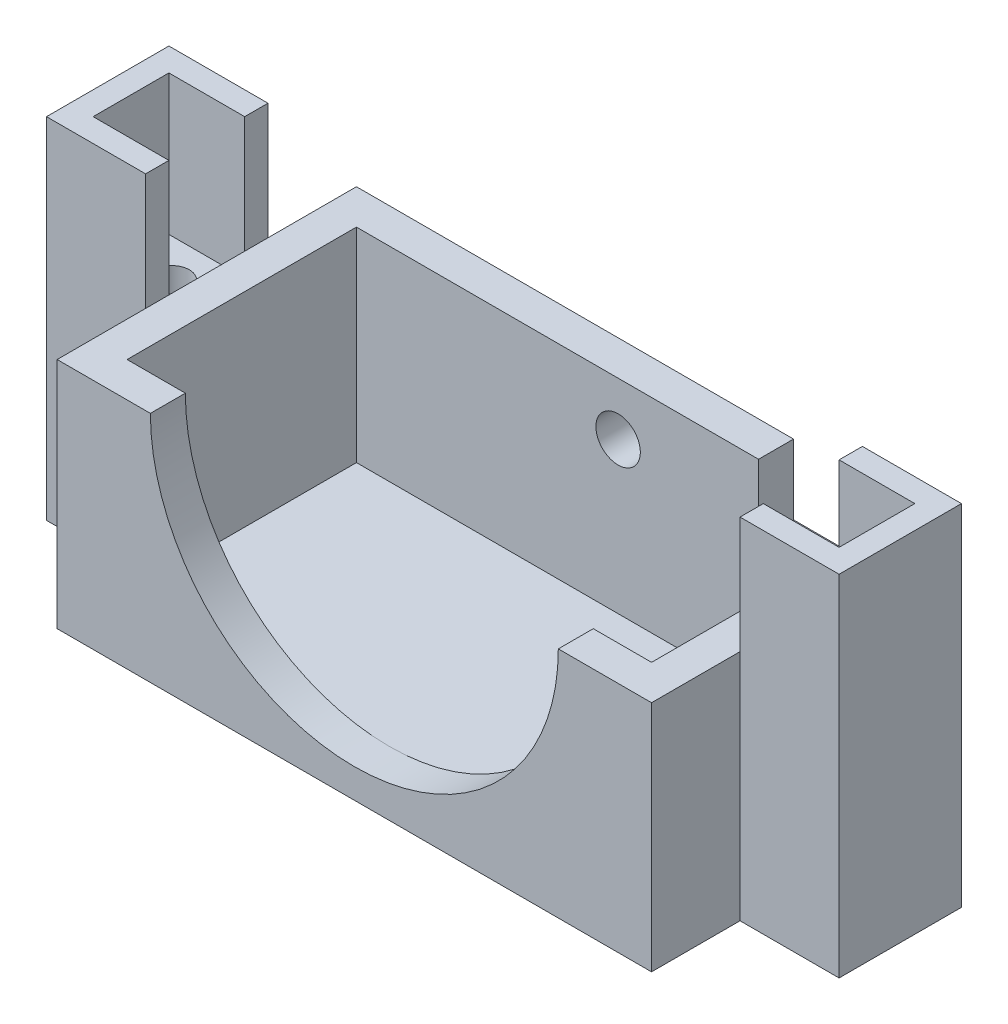
SolidWorks part; units mm, degrees
ref_plane "Front" through (0, 0, 0) normal (0, 0, 1) x (1, 0, 0)
ref_plane "Top" through (0, 0, 0) normal (0, 1, 0) x (1, 0, 0)
ref_plane "Right" through (0, 0, 0) normal (1, 0, 0) x (0, 0, -1)
sketch "Sketch1" plane through (0, 0, 0) normal (0, 1, 0) x (1, 0, 0)
  line L1 (-22.5, -9.84) -> (22.5, -9.84) construction
  line L2 (-22.5, -9.84) -> (-22.5, 9.84) construction
  line L3 (-22.5, 9.84) -> (22.5, 9.84) construction
  line L4 (22.5, -9.84) -> (22.5, 9.84) construction
  line L5 (-25.5, -12.84) -> (25.5, -12.84)
  line L6 (-25.5, -12.84) -> (-25.5, 12.84)
  line L7 (-25.5, 12.84) -> (25.5, 12.84)
  line L8 (25.5, -12.84) -> (25.5, 12.84)
  line L9 (-25.5, -12.84) -> (25.5, 12.84) construction
  line L10 (-25.5, 12.84) -> (25.5, -12.84) construction
  point P1 (0, 0)
  point P6 (0, 0)
  point P7 (0, 0)
  dimension "D1" = 45
  dimension "D2" = 19.68
  dimension "D3" = 3
  dimension "D4" = 3
  dimension "D5" = 3
  dimension "D6" = 3
extrude "Boss-Extrude1" add sketch "Sketch1" along normal blind 20
sketch "Sketch2" plane through (0, 20, 0) normal (0, 1, 0) x (1, 0, 0)
  line L1 (-22.5, -9.84) -> (22.5, -9.84)
  line L2 (-22.5, -9.84) -> (-22.5, 9.84)
  line L3 (-22.5, 9.84) -> (22.5, 9.84)
  line L4 (22.5, -9.84) -> (22.5, 9.84)
  line L5 (-22.5, -9.84) -> (22.5, 9.84) construction
  line L6 (-22.5, 9.84) -> (22.5, -9.84) construction
  point P0 (0, 0)
  dimension "D1" = 45
  dimension "D2" = 19.68
extrude "Cut-Extrude1" cut sketch "Sketch2" against normal blind 17.5
sketch "Sketch9" plane through (0, 0, 12.84) normal (0, 0, 1) x (1, 0, 0)
  line L0 (-25.5, 20) -> (25.5, 20) construction
  line L1 (-17.5, 20) -> (17.5, 20)
  arc A0 (-17.5, 20) -> (17.5, 20) centre (0, 20) ccw
  dimension "D1" = 35
extrude "Cut-Extrude5" cut sketch "Sketch9" against normal up to surface (3 mm away) up to face at (0, 11.25, 9.84)
sketch "Sketch10" plane through (0, 0, -12.84) normal (0, 0, -1) x (-1, 0, 0)
  line L0 (-25.5, 0) -> (25.5, 0) construction
  line L1 (-22, 2.5) -> (22, 2.5) construction
  line L2 (-22, 2.5) -> (-22, 20) construction
  line L3 (-22, 20) -> (22, 20) construction
  line L4 (22, 2.5) -> (22, 20) construction
  line L5 (-25.5, 20) -> (-25.5, 0) construction
  line L6 (-22, 14) -> (-12, 14)
  line L7 (-12, 14) -> (-12, 20)
  line L8 (-22, 20) -> (-22, 14)
  line L9 (-22, 20) -> (-12, 20)
  circle A0 centre (0.05, 15.45) radius 1.9054
  dimension "D1" = 2.5
  dimension "D2" = 3.5
  dimension "D3" = 44
  dimension "D4" = 17.5
  dimension "D5" = 12.95
  dimension "D6" = 22.05
  dimension "D7" = 10
  dimension "D8" = 6
extrude "Cut-Extrude6" cut sketch "Sketch10" against normal up to surface (3 mm away) up to face at (0, 11.25, -9.84)
sketch "Sketch11" plane through (0, 0, 0) normal (0, -1, 0) x (1, 0, 0)
  line L0 (-25.5, 0) -> (25.5, 0) construction
  line L1 (-25.5, -12.84) -> (-25.5, 12.84) construction
  line L2 (25.5, 12.84) -> (25.5, -12.84) construction
  line L3 (0, -12.84) -> (0, 12.84) construction
  line L4 (25.5, -12.84) -> (-25.5, -12.84) construction
  line L5 (-25.5, 12.84) -> (25.5, 12.84) construction
  line L6 (-25.5, -3.25) -> (-32, -3.25)
  line L7 (-32, -3.25) -> (-32, 3.25)
  line L8 (-32, 3.25) -> (-25.5, 3.25)
  line L9 (25.5, -3.25) -> (25.5, 3.25)
  line L10 (-25.5, -3.25) -> (-25.5, 3.25)
  line L11 (32, 3.25) -> (25.5, 3.25)
  line L12 (32, -3.25) -> (32, 3.25)
  line L13 (25.5, -3.25) -> (32, -3.25)
  circle A0 centre (-28.5, 0) radius 1.5
  circle A1 centre (28.5, 0) radius 1.5
  dimension "D1" = 3
  dimension "D2" = 3
  dimension "D3" = 6.5
  dimension "D4" = 6.5
extrude "Boss-Extrude4" add sketch "Sketch11" against normal blind 18
sketch "Sketch12" plane through (0, 0, 0) normal (0, -1, 0) x (1, 0, 0)
  line L0 (0, -12.84) -> (0, 12.84) construction
  line L1 (25.5, -12.84) -> (-25.5, -12.84) construction
  line L2 (-25.5, 12.84) -> (25.5, 12.84) construction
  line L3 (-32, 0) -> (32, 0) construction
  line L6 (-32, 3.25) -> (-32, -3.25) construction
  line L7 (32, -3.25) -> (32, 3.25) construction
  line L8 (-25.5, -3.25) -> (-25.5, -5.25)
  line L9 (-25.5, -12.84) -> (-25.5, -3.25) construction
  line L10 (-32, 0) -> (-34, 0) construction
  line L11 (-25.5, -5.25) -> (-34, -5.25)
  line L12 (-25.5, 3.25) -> (-25.5, 5.25)
  line L13 (-25.5, 3.25) -> (-25.5, 12.84) construction
  line L14 (-34, -5.25) -> (-34, 5.25)
  line L15 (-34, 5.25) -> (-25.5, 5.25)
  line L16 (-25.5, -3.25) -> (-32, -3.25)
  line L17 (-32, -3.25) -> (-32, 3.25)
  line L18 (-25.5, 3.25) -> (-32, 3.25) construction
  line L19 (-25.5, 3.25) -> (-32, 3.25)
  line L20 (32, 0) -> (34, 0) construction
  line L21 (25.5, 3.25) -> (32, 3.25)
  line L22 (32, -3.25) -> (32, 3.25)
  line L23 (25.5, -3.25) -> (32, -3.25)
  line L24 (34, 5.25) -> (25.5, 5.25)
  line L25 (34, -5.25) -> (34, 5.25)
  line L26 (25.5, 3.25) -> (25.5, 5.25)
  line L27 (25.5, -5.25) -> (34, -5.25)
  line L28 (25.5, -3.25) -> (25.5, -5.25)
  dimension "D1" = 2
  dimension "D2" = 2
extrude "Boss-Extrude5" add sketch "Sketch12" against normal blind 30
